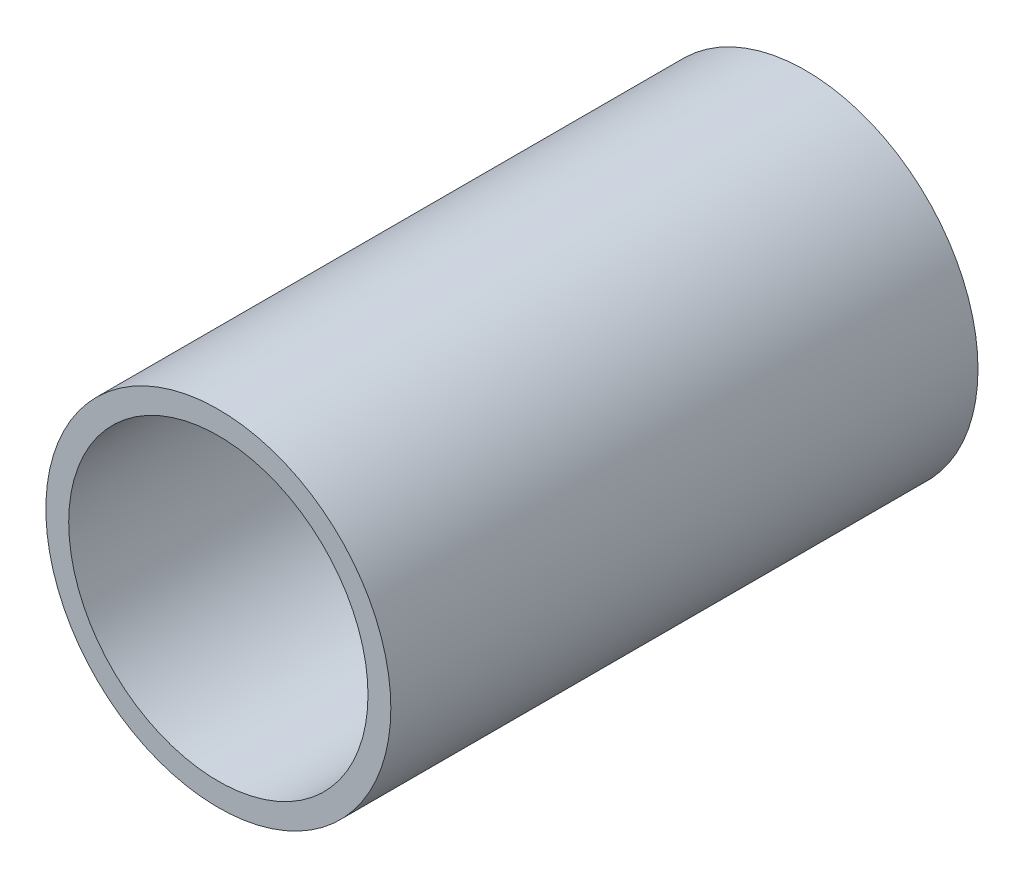
SolidWorks part; units mm, degrees
ref_plane "Front Plane" through (0, 0, 0) normal (0, 0, 1) x (1, 0, 0)
ref_plane "Top Plane" through (0, 0, 0) normal (0, 1, 0) x (1, 0, 0)
ref_plane "Right Plane" through (0, 0, 0) normal (1, 0, 0) x (0, 0, -1)
sketch "Sketch1" plane through (0, 0, 0) normal (0, 0, 1) x (1, 0, 0)
  circle A0 centre (0, 0) radius 6.55
  circle A1 centre (0, 0) radius 7.55
  point P4 (0, 0)
  dimension "D1" = 15.1
  dimension "D2" = 13.1
extrude "Boss-Extrude1" add sketch "Sketch1" along normal blind 25.7
